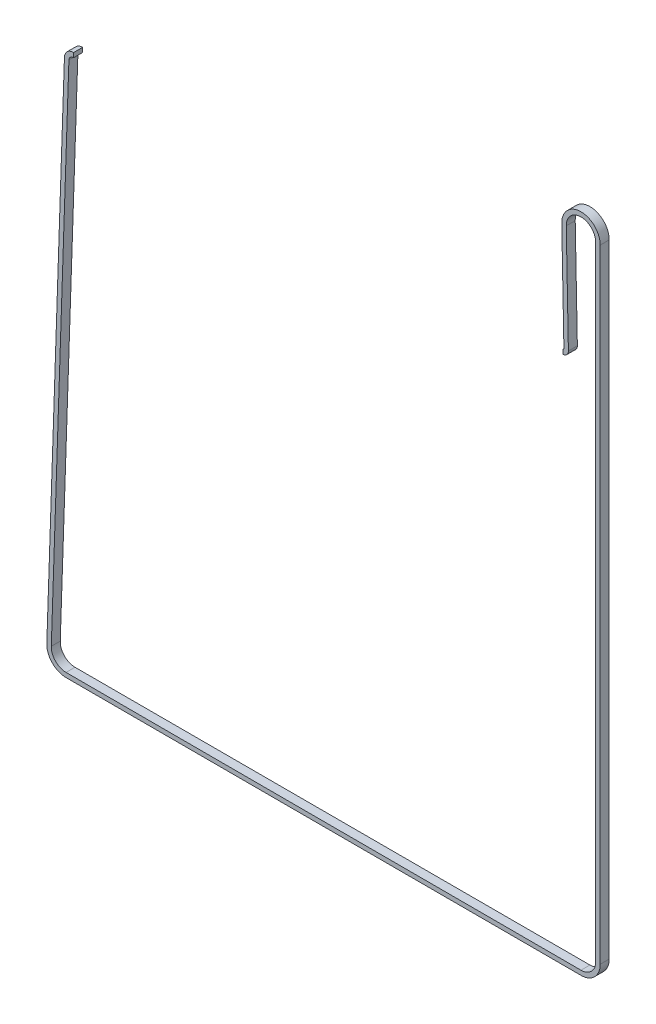
SolidWorks part; units mm, degrees
ref_plane "Front Plane" through (0, 0, 0) normal (0, 0, 1) x (1, 0, 0)
ref_plane "Top Plane" through (0, 0, 0) normal (0, 1, 0) x (1, 0, 0)
ref_plane "Right Plane" through (0, 0, 0) normal (1, 0, 0) x (0, 0, -1)
sketch "Sketch2" plane through (0, 0, 0) normal (0, 0, 1) x (1, 0, 0)
  line L0 (0, 0) -> (1, 0) construction
  line L1 (0, 0) -> (0, 1) construction
  line L2 (3.6743, 0.0734) -> (2.2392, 71.9437)
  line L3 (21.9872, 72.1408) -> (21.9872, -344.8449)
  line L4 (12.1043, -354.7199) -> (-332.6577, -354.4438)
  line L5 (-342.519, -344.2321) -> (-330.7194, 1.6025)
  line L6 (-327.6464, 4.4993) -> (-0.0917, -3.6739)
  arc A0 (-0.0917, -3.6739) -> (3.6743, 0.0734) centre (0, 0) ccw
  arc A1 (2.2392, 71.9437) -> (21.9872, 72.1408) centre (12.1122, 72.1408) cw
  arc A2 (21.9872, -344.8449) -> (12.1043, -354.7199) centre (12.1122, -344.8449) cw
  arc A3 (-332.6577, -354.4438) -> (-342.519, -344.2321) centre (-332.6498, -344.5688) cw
  arc A4 (-330.7194, 1.6025) -> (-327.6464, 4.4993) centre (-327.7212, 1.5002) cw
extrude "Extrude-Thin1" add sketch "Sketch2" along normal blind 6 thin thin type one direction wall 3
sketch "Sketch3" plane through (0, 0, 0) normal (0, 0, 1) x (1, 0, 0)
  line L0 (-0.0917, -3.6739) -> (-327.6464, 4.4993) construction
  line L1 (-327.5715, 7.4984) -> (0.0001, 7.4984)
  line L2 (-327.5715, 7.4984) -> (-327.5715, -3.6761)
  line L3 (-327.5715, -3.6761) -> (0.0001, -3.6761)
  line L4 (0.0001, 7.4984) -> (0.0001, -3.6761)
  line L5 (-163.7857, -3.6761) -> (-163.7857, 7.4984) construction
  line L6 (-327.5715, 1.9111) -> (0.0001, 1.9111) construction
  point P6 (0, -3.6761)
  point P7 (-327.6214, 5.499)
  point P100 (-163.7857, 1.9111)
extrude "Cut-Extrude3" cut sketch "Sketch3" along normal through all
